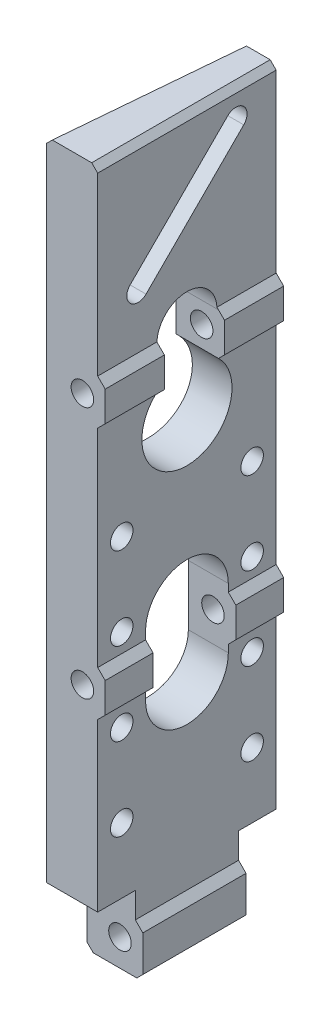
SolidWorks part; units mm, degrees
ref_plane "Front Plane" through (0, 0, 0) normal (0, 0, 1) x (1, 0, 0)
ref_plane "Top Plane" through (0, 0, 0) normal (0, 1, 0) x (1, 0, 0)
ref_plane "Right Plane" through (0, 0, 0) normal (1, 0, 0) x (0, 0, -1)
sketch "Sketch1" plane through (0, 0, 0) normal (1, 0, 0) x (0, 0, -1)
  line L0 (0, 0) -> (0, 31.75)
  line L1 (0, 31.75) -> (-15.9004, 31.75)
  line L5 (-15.9004, 304.8) -> (59.5376, 304.8)
  line L6 (59.5376, 304.8) -> (59.5376, 31.75)
  line L9 (59.5376, 31.75) -> (43.6372, 31.75)
  line L10 (43.6372, 31.75) -> (43.6372, 0)
  line L11 (43.6372, 0) -> (0, 0)
  line L15 (-15.9004, 31.75) -> (-15.9004, 304.8)
  dimension "D1" = 43.6372
  dimension "D3" = 75.438
  dimension "D4" = 304.8
  dimension "D5" = 31.75
extrude "Boss-Extrude1" add sketch "Sketch1" along normal blind 24.892
sketch "Sketch11" plane through (24.892, 0, 0) normal (1, 0, 0) x (0, 0, -1)
  line L0 (21.8186, 124.46) -> (21.8186, 99.06) construction
  line L1 (39.3065, 124.46) -> (39.3065, 99.06)
  line L2 (4.3307, 124.46) -> (4.3307, 99.06)
  line L3 (34.5186, 227.33) -> (34.5186, 209.55)
  line L4 (9.1186, 227.33) -> (9.1186, 209.55)
  line L5 (9.1186, 218.44) -> (34.5186, 218.44) construction
  line L6 (21.8186, 227.33) -> (21.8186, 304.8) construction
  line L7 (59.5376, 304.8) -> (-15.9004, 304.8) construction
  line L8 (21.8186, 218.44) -> (21.8186, 227.33) construction
  line L9 (0, 0) -> (43.6372, 0) construction
  line L10 (21.8186, 218.44) -> (21.8186, 111.76) construction
  arc A0 (39.3065, 124.46) -> (4.3307, 124.46) centre (21.8186, 124.46) ccw
  arc A1 (4.3307, 99.06) -> (39.3065, 99.06) centre (21.8186, 99.06) ccw
  arc A2 (9.1186, 227.33) -> (34.5186, 227.33) centre (21.8186, 227.33) cw
  arc A3 (9.1186, 209.55) -> (34.5186, 209.55) centre (21.8186, 195.351) ccw
  point P2 (21.8186, 111.76)
  point P20 (21.8186, 0)
  dimension "D3" = 19.05
  dimension "D1" = 25.4
  dimension "D2" = 25.4
  dimension "D4" = 111.76
  dimension "D5" = 17.78
  dimension "D6" = 34.9758
  dimension "D7" = 106.68
extrude "Cut-Extrude8" cut sketch "Sketch11" against normal through all
sketch "Sketch8" plane through (0, 0, 0) normal (0, 1, 0) x (1, 0, 0)
  line L0 (0, 59.5376) -> (6.6, 59.5376)
  line L3 (0, -15.9004) -> (0, 59.5376)
  line L5 (6.6, 59.5376) -> (0, -15.9004)
  dimension "D1" = 5
extrude "Cut-Extrude6" cut sketch "Sketch8" along normal through all
sketch "Sketch9" plane through (0, 0, 15.9004) normal (0, 0, 1) x (1, 0, 0)
  line L2 (24.892, 304.8) -> (24.892, 31.75) construction
  line L3 (24.892, 0) -> (1.3911, 0) construction
  circle A0 centre (15.24, 218.44) radius 4.7625
  dimension "D1" = 9.652
  dimension "D3" = 9.525
  dimension "D2" = 218.44
extrude "Cut-Extrude7" cut sketch "Sketch9" against normal mid plane 152.4
sketch "Sketch2" plane through (0, 0, 15.9004) normal (0, 0, 1) x (1, 0, 0)
  line L0 (20.0025, 111.76) -> (20.0025, 218.44) construction
  line L1 (15.24, 111.76) -> (15.24, 218.44) construction
  line L2 (15.24, 218.44) -> (20.0025, 218.44) construction
  line L3 (24.892, 0) -> (1.3911, 0) construction
  circle A0 centre (15.24, 111.76) radius 4.7625
  circle A1 centre (15.24, 218.44) radius 4.7625 construction
  point P4 (13.1416, 0)
  dimension "D2" = 111.76
extrude "Cut-Extrude1" cut sketch "Sketch2" against normal through all
sketch "Sketch3" plane through (0, 0, 0) normal (0, 0, 1) x (1, 0, 0)
  line L1 (24.892, 0) -> (1.3911, 0) construction
  line L2 (15.24, 11.43) -> (15.24, 111.76) construction
  circle A0 centre (15.24, 11.43) radius 4.7625
  dimension "D1" = 9.525
  dimension "D2" = 11.43
extrude "Cut-Extrude2" cut sketch "Sketch3" against normal through all
sketch "Sketch12" plane through (24.892, 0, 0) normal (1, 0, 0) x (0, 0, -1)
  line L0 (1.164, 251.1254) -> (42.4732, 292.4346) construction
  line L1 (-2.2036, 254.493) -> (39.1056, 295.8022)
  line L2 (4.5316, 247.7578) -> (45.8408, 289.067)
  line L3 (21.8186, 271.78) -> (21.8186, 304.8) construction
  line L5 (59.5376, 304.8) -> (-15.9004, 304.8) construction
  arc A0 (-2.2036, 254.493) -> (4.5316, 247.7578) centre (1.164, 251.1254) ccw
  arc A1 (45.8408, 289.067) -> (39.1056, 295.8022) centre (42.4732, 292.4346) ccw
  point P2 (21.8186, 271.78)
  dimension "D1" = 9.525
  dimension "D2" = 33.02
  dimension "D3" = 58.42
  dimension "D4" = 45
extrude "Cut-Extrude9" cut sketch "Sketch12" against normal through all
sketch "Sketch13" plane through (0, 0, 15.9004) normal (0, 0, 1) x (1, 0, 0)
  line L0 (21.717, 304.8) -> (21.717, 227.965)
  line L1 (24.892, 304.8) -> (0, 304.8) construction
  line L2 (21.717, 227.965) -> (24.892, 224.79)
  line L3 (24.892, 304.8) -> (24.892, 31.75) construction
  line L4 (24.892, 224.79) -> (24.892, 304.8)
  line L5 (24.892, 212.09) -> (24.892, 118.11)
  line L6 (24.892, 118.11) -> (21.717, 121.285)
  line L7 (21.717, 121.285) -> (21.717, 208.915)
  line L8 (21.717, 208.915) -> (24.892, 212.09)
  line L9 (24.892, 105.41) -> (21.717, 102.235)
  line L10 (21.717, 102.235) -> (21.717, 20.955)
  line L11 (21.717, 20.955) -> (24.892, 17.78)
  line L12 (24.892, 17.78) -> (24.892, 105.41)
  line L13 (24.892, 224.79) -> (24.892, 212.09) construction
  line L14 (24.892, 218.44) -> (15.24, 218.44) construction
  line L15 (24.892, 105.41) -> (24.892, 118.11) construction
  line L16 (24.892, 111.76) -> (15.24, 111.76) construction
  line L17 (15.24, 11.43) -> (24.892, 11.43) construction
  line L18 (24.892, 17.78) -> (24.892, 5.08) construction
  line M5 (24.892, 31.75) -> (24.892, 304.8)
  line M6 (24.892, 304.8) -> (0, 304.8)
  dimension "D1" = 45
  dimension "D2" = 45
  dimension "D3" = 45
  dimension "D4" = 3.175
  dimension "D5" = 12.7
extrude "Cut-Extrude10" cut sketch "Sketch13" against normal through all contours L0 L2 M5 M6 | L7 L8 L5 L6 | L12 L9 L10 L11
sketch "Sketch6" plane through (24.892, 0, 0) normal (1, 0, 0) x (0, 0, -1)
  line L1 (-5.7404, 94.2975) -> (49.3776, 94.2975) construction
  line L2 (-15.9004, 118.11) -> (-15.9004, 105.41) construction
  line L4 (-15.9004, 304.8) -> (-15.9004, 31.75) construction
  line L5 (-5.7404, 99.06) -> (49.3776, 99.06) construction
  line L6 (21.8186, 94.2975) -> (21.8186, 17.78) construction
  line L7 (43.6372, 17.78) -> (0, 17.78) construction
  circle A0 centre (-5.7404, 94.2975) radius 4.7625
  circle A1 centre (49.3776, 94.2975) radius 4.7625
  point P4 (-15.9004, 111.76)
  dimension "D1" = 17.4625
  dimension "D3" = 9.525
  dimension "D2" = 10.16
extrude "Cut-Extrude4" cut sketch "Sketch6" against normal through all
pattern_linear "LPattern1" count 3 spacing 34.925 along (0, 1, 0) count 2 spacing 34.925 along (0, -1, 0) of "Cut-Extrude4"
chamfer "Chamfer1" distance 2.54 angle 45 4 edges at (3.3, 304.8, -21.8186) (3.3, 0, -21.8186) (24.892, 0, -21.8186) (21.717, 304.8, -21.8186)
